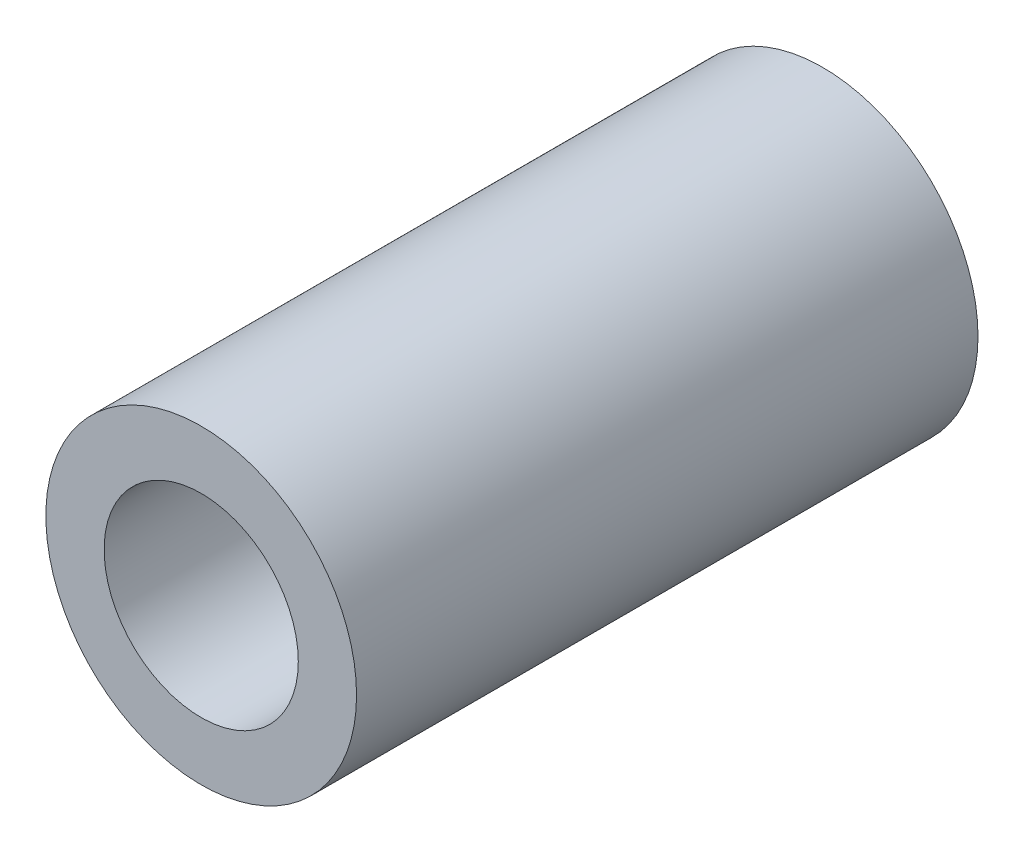
SolidWorks part; units mm, degrees
ref_plane "Front Plane" through (0, 0, 0) normal (0, 0, 1) x (1, 0, 0)
ref_plane "Top Plane" through (0, 0, 0) normal (0, 1, 0) x (1, 0, 0)
ref_plane "Right Plane" through (0, 0, 0) normal (1, 0, 0) x (0, 0, -1)
sketch "Sketch1" plane through (0, 0, 0) normal (0, 0, 1) x (1, 0, 0)
  circle A0 centre (0, 0) radius 1.5875
extrude "Boss-Extrude1" add sketch "Sketch1" along normal blind 6.35 contours A0
sketch "Sketch2" plane through (0, 0, 6.35) normal (0, 0, 1) x (1, 0, 0)
  circle A0 centre (0, 0) radius 0.9922
extrude "Cut-Extrude1" cut sketch "Sketch2" against normal up to next
